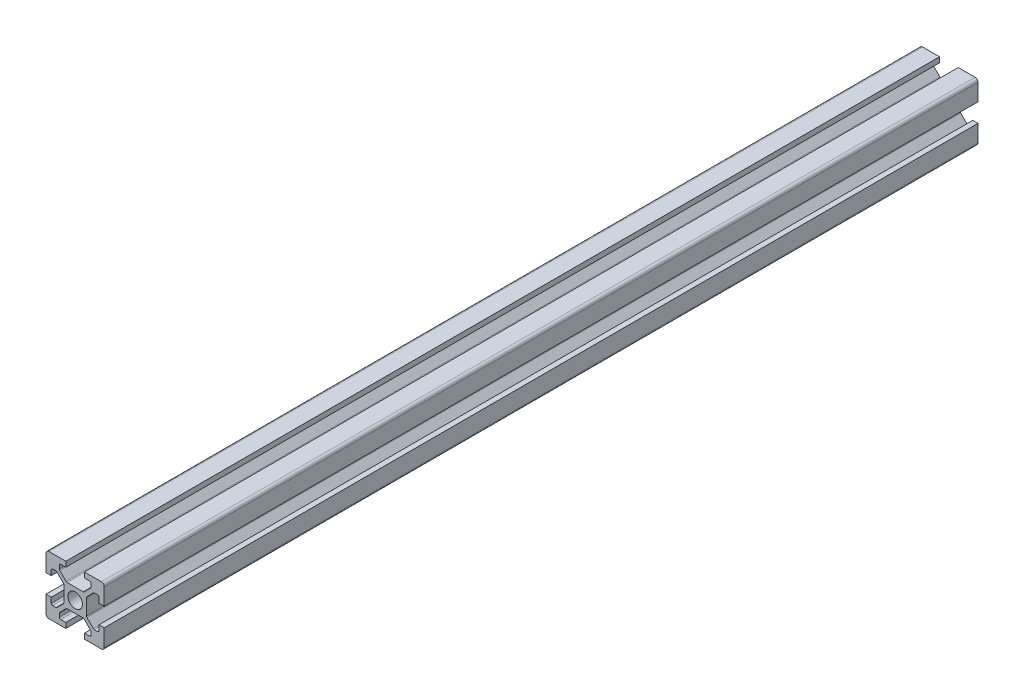
SolidWorks part; units mm, degrees
material "1060 Alloy"
ref_plane "Front Plane" through (0, 0, 0) normal (0, 0, 1) x (1, 0, 0)
ref_plane "Top Plane" through (0, 0, 0) normal (0, 1, 0) x (1, 0, 0)
ref_plane "Right Plane" through (0, 0, 0) normal (1, 0, 0) x (0, 0, -1)
sketch "Sketch1" plane through (0, 0, 0) normal (0, 0, 1) x (1, 0, 0)
  line L0 (20, 0) -> (-8.059, 28.059) construction
  line L1 (0, 0) -> (6.8, 0)
  line L2 (0, 0) -> (0, 6.8)
  line L3 (0, 20) -> (6.8, 20)
  line L4 (20, 0) -> (20, 6.8)
  line L5 (6.8, 20) -> (6.8, 18.2)
  line L6 (20, 20) -> (8.2322, 8.2322) construction
  line L7 (12.95, 6.1) -> (7.05, 6.1)
  line L8 (13.9, 7.05) -> (13.9, 12.95)
  line L9 (12.95, 13.9) -> (7.05, 13.9)
  line L10 (6.1, 7.05) -> (6.1, 12.95)
  line L11 (13.9, 6.1) -> (6.1, 13.9) construction
  line L12 (13.9, 13.9) -> (6.1, 6.1) construction
  line L13 (4.55, 16.4) -> (7.05, 13.9)
  line L14 (13.2, 18.2) -> (13.2, 20)
  line L15 (1.8, 6.8) -> (0, 6.8)
  line L16 (0, 13.2) -> (0, 20)
  line L17 (0, 13.2) -> (1.8, 13.2)
  line L18 (10, 10) -> (10, 13.9) construction
  line L19 (16.4, 4.55) -> (13.9, 7.05)
  line L20 (4.55, 16.4) -> (4.55, 18.2)
  line L21 (4.55, 18.2) -> (6.8, 18.2)
  line L22 (13.2, 18.2) -> (15.45, 18.2)
  line L23 (15.45, 18.2) -> (15.45, 16.4)
  line L24 (15.45, 16.4) -> (12.95, 13.9)
  line L25 (16.4, 4.55) -> (18.2, 4.55)
  line L26 (18.2, 4.55) -> (18.2, 6.8)
  line L27 (20, 6.8) -> (18.2, 6.8)
  line L28 (18.2, 13.2) -> (20, 13.2)
  line L29 (18.2, 13.2) -> (18.2, 15.45)
  line L30 (18.2, 15.45) -> (16.4, 15.45)
  line L31 (16.4, 15.45) -> (13.9, 12.95)
  line L32 (1.8, 4.55) -> (3.6, 4.55)
  line L33 (3.6, 15.45) -> (6.1, 12.95)
  line L34 (3.6, 15.45) -> (1.8, 15.45)
  line L35 (1.8, 15.45) -> (1.8, 13.2)
  line L36 (0, 13.2) -> (1.8, 13.2)
  line L37 (1.8, 6.8) -> (0, 6.8)
  line L38 (3.6, 4.55) -> (6.1, 7.05)
  line L39 (1.8, 6.8) -> (1.8, 4.55)
  line L40 (15.45, 3.6) -> (12.95, 6.1)
  line L41 (4.55, 3.6) -> (7.05, 6.1)
  line L42 (4.55, 1.8) -> (4.55, 3.6)
  line L43 (6.8, 1.8) -> (4.55, 1.8)
  line L44 (6.8, 1.8) -> (6.8, 0)
  line L45 (15.45, 3.6) -> (15.45, 1.8)
  line L46 (15.45, 1.8) -> (13.2, 1.8)
  line L47 (13.2, 0) -> (13.2, 1.8)
  line L48 (13.2, 20) -> (20, 20)
  line L49 (20, 13.2) -> (20, 20)
  line L50 (13.2, 0) -> (20, 0)
  line L51 (6.1, 6.1) -> (-5.5045, -5.5045) construction
  circle A0 centre (10, 10) radius 2.5
  point P25 (10, 16.4)
  point P39 (13.2, 19.1)
  point P46 (0.9, 6.8)
  dimension "D3" = 5
  dimension "D2" = 20
  dimension "D4" = 7.8
  dimension "D5" = 7.8
  dimension "D6" = 6.8
  dimension "D7" = 6.8
  dimension "D8" = 1.8
  dimension "D9" = 10.9
  dimension "D10" = 1.8
  dimension "D11" = 10.9
  dimension "D12" = 20
extrude "Boss-Extrude1" add sketch "Sketch1" along normal blind 300 contours L47 L50 L4 L27 L26 L25 L19 L8 L31 L30 L29 L28 L49 L48 L14 L22 L23 L24 L9 L13 L20 L21 L5 L3 L16 L17 L35 L34 L33 L10 L38 L32 L39 L15 L2 L1 L44 L43 L42 L41 L7 L40 L45 L46 A0
fillet "Fillet1" radius 1 4 edges at (20, 20, 150) (20, 0, 150) (0, 0, 150) (0, 20, 150)
fillet "Fillet2" radius 0.5 6 edges at (4.55, 18.2, 150) (4.55, 16.4, 150) (7.05, 13.9, 150) (15.45, 18.2, 150) (15.45, 16.4, 150) (12.95, 13.9, 150)
fillet "Fillet3" radius 0.5 6 edges at (18.2, 15.45, 150) (16.4, 15.45, 150) (13.9, 12.95, 150) (18.2, 4.55, 150) (13.9, 7.05, 150) (16.4, 4.55, 150)
fillet "Fillet4" radius 0.5 6 edges at (1.8, 15.45, 150) (3.6, 15.45, 150) (6.1, 12.95, 150) (3.6, 4.55, 150) (1.8, 4.55, 150) (6.1, 7.05, 150)
fillet "Fillet5" radius 0.5 6 edges at (7.05, 6.1, 150) (4.55, 3.6, 150) (4.55, 1.8, 150) (15.45, 1.8, 150) (15.45, 3.6, 150) (12.95, 6.1, 150)
